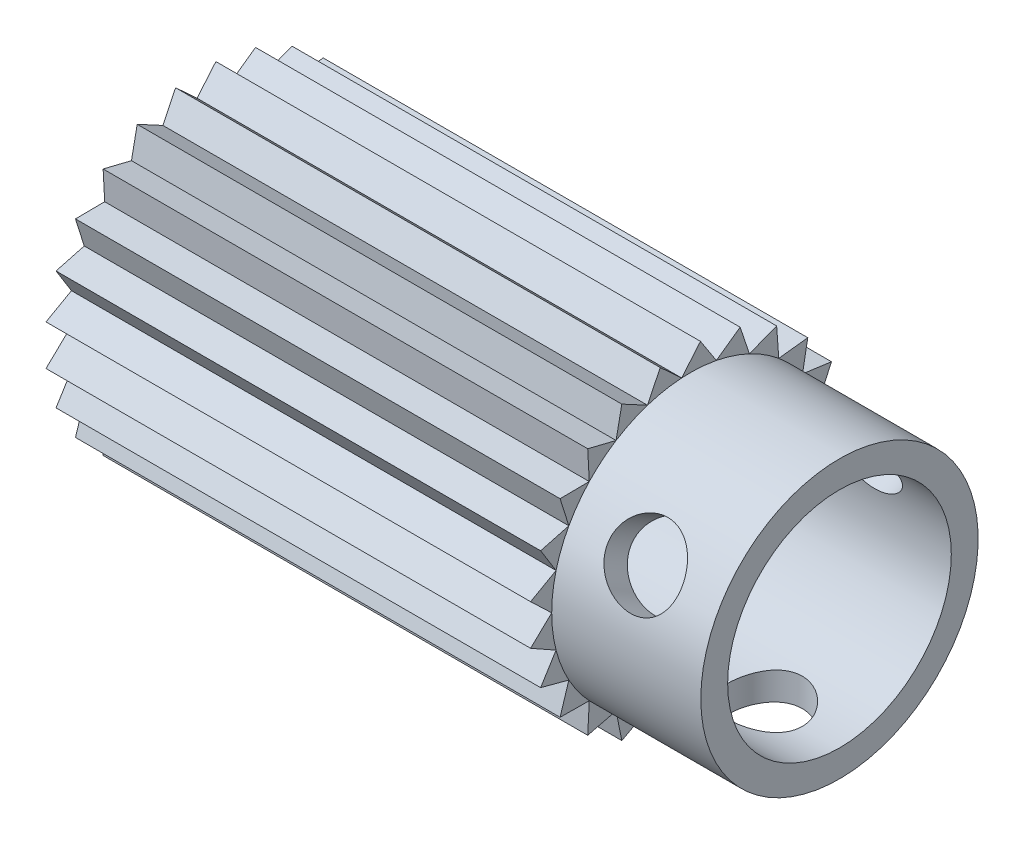
SolidWorks part; units mm, degrees
material "AISI 1020"
ref_plane "X-Y Datum" through (0, 0, 0) normal (0, 0, 1) x (1, 0, 0)
ref_plane "X-Z Datum" through (0, 0, 0) normal (0, 1, 0) x (1, 0, 0)
ref_plane "Y-Z Datum" through (0, 0, 0) normal (1, 0, 0) x (0, 0, -1)
sketch "Sketch1" plane through (0, 0, 0) normal (0, 1, 0) x (1, 0, 0)
  line L0 (-42.0666, 0) -> (42.0666, 0) construction
  line L1 (-30.1625, -15.875) -> (-30.1625, -6.35)
  line L3 (23.8125, -9.525) -> (23.8125, -11.811)
  line L4 (23.8125, -11.811) -> (11.1125, -11.811)
  line L5 (11.1125, -11.811) -> (11.1125, -15.875)
  line L6 (11.1125, -15.875) -> (-30.1625, -15.875)
  line L7 (-30.1625, -6.35) -> (-23.8125, -6.35)
  line L8 (-23.8125, -6.35) -> (-23.8125, -9.525)
  line L9 (-23.8125, -9.525) -> (23.8125, -9.525)
  point P4 (0, -9.525)
  dimension "D1" = 41.275
  dimension "D2" = 6.35
  dimension "D3" = 6.35
  dimension "D4" = 9.525
  dimension "D5" = 11.811
  dimension "D6" = 15.875
  dimension "D7" = 53.975
revolve "Revolve1" add sketch "Sketch1" angle 360 about L0
sketch "Sketch2" plane through (0, 0, 0) normal (0, 1, 0) x (1, 0, 0)
  line L0 (23.8125, -11.811) -> (11.1125, -11.811) construction
  circle A0 centre (17.4625, 0) radius 3.175
  point P7 (17.4625, -11.811)
  dimension "D1" = 6.35
extrude "Cut-Extrude1" cut sketch "Sketch2" against normal through all
pattern_circular "CirPattern1" count 3 over 360 about axis through (-42.0666, 0, 0) along (1, 0, 0) of "Cut-Extrude1"
sketch "Sketch3" plane through (-30.1625, 0, 0) normal (-1, 0, 0) x (0, 0, 1)
  line L0 (0, 0) -> (15.875, 0) construction
  line L2 (15.7498, 1.9897) -> (0, 0) construction
  line L3 (0, 0) -> (15.3763, 3.948) construction
  line L4 (11.811, 0) -> (13.6078, 1.7191)
  line L5 (13.6078, 1.7191) -> (11.4399, 2.9373)
  line L6 (13.6078, -1.7191) -> (11.811, 0)
  line L7 (11.4399, -2.9373) -> (13.6078, -1.7191)
  line L8 (12.7528, -5.0492) -> (11.4399, -2.9373)
  line L9 (10.3501, -5.69) -> (12.7528, -5.0492)
  line L10 (11.0965, -8.0621) -> (10.3501, -5.69)
  line L11 (8.6098, -8.0852) -> (11.0965, -8.0621)
  line L12 (8.7429, -10.5684) -> (8.6098, -8.0852)
  line L13 (6.3287, -9.9724) -> (8.7429, -10.5684)
  line L14 (5.84, -12.4106) -> (6.3287, -9.9724)
  line L15 (3.6498, -11.2329) -> (5.84, -12.4106)
  line L16 (2.5701, -13.4731) -> (3.6498, -11.2329)
  line L17 (0.7416, -11.7877) -> (2.5701, -13.4731)
  line L18 (-0.8612, -13.6889) -> (0.7416, -11.7877)
  line L19 (-2.2132, -11.6018) -> (-0.8612, -13.6889)
  line L20 (-4.2385, -13.0447) -> (-2.2132, -11.6018)
  line L21 (-5.0289, -10.6869) -> (-4.2385, -13.0447)
  line L22 (-7.3494, -11.5808) -> (-5.0289, -10.6869)
  line L23 (-7.5286, -9.1005) -> (-7.3494, -11.5808)
  line L24 (-9.9985, -9.3892) -> (-7.5286, -9.1005)
  line L25 (-9.5553, -6.9423) -> (-9.9985, -9.3892)
  line L26 (-12.0194, -6.6077) -> (-9.5553, -6.9423)
  line L27 (-10.9816, -4.3479) -> (-12.0194, -6.6077)
  line L28 (-13.2851, -3.411) -> (-10.9816, -4.3479)
  line L29 (-11.7179, -1.4803) -> (-13.2851, -3.411)
  line L30 (-13.716, 0) -> (-11.7179, -1.4803)
  line L31 (-11.7179, 1.4803) -> (-13.716, 0)
  line L32 (-13.2851, 3.411) -> (-11.7179, 1.4803)
  line L33 (-10.9816, 4.3479) -> (-13.2851, 3.411)
  line L34 (-12.0194, 6.6077) -> (-10.9816, 4.3479)
  line L35 (-9.5553, 6.9423) -> (-12.0194, 6.6077)
  line L36 (-9.9985, 9.3892) -> (-9.5553, 6.9423)
  line L37 (-7.5286, 9.1005) -> (-9.9985, 9.3892)
  line L38 (-7.3494, 11.5808) -> (-7.5286, 9.1005)
  line L39 (-5.0289, 10.6869) -> (-7.3494, 11.5808)
  line L40 (-4.2385, 13.0447) -> (-5.0289, 10.6869)
  line L41 (-2.2132, 11.6018) -> (-4.2385, 13.0447)
  line L42 (-0.8612, 13.6889) -> (-2.2132, 11.6018)
  line L43 (0.7416, 11.7877) -> (-0.8612, 13.6889)
  line L44 (2.5701, 13.4731) -> (0.7416, 11.7877)
  line L45 (3.6498, 11.2329) -> (2.5701, 13.4731)
  line L46 (5.84, 12.4106) -> (3.6498, 11.2329)
  line L47 (6.3287, 9.9724) -> (5.84, 12.4106)
  line L48 (8.7429, 10.5684) -> (6.3287, 9.9724)
  line L49 (8.6098, 8.0852) -> (8.7429, 10.5684)
  line L50 (11.0965, 8.0621) -> (8.6098, 8.0852)
  line L51 (10.3501, 5.69) -> (11.0965, 8.0621)
  line L52 (12.7528, 5.0492) -> (10.3501, 5.69)
  line L53 (11.4399, 2.9373) -> (12.7528, 5.0492)
  circle A0 centre (0, 0) radius 15.875 construction
  circle A1 centre (0, 0) radius 11.811 construction
  circle A2 centre (0, 0) radius 13.716 construction
  circle A3 centre (0, 0) radius 11.811 construction
  arc A4 (11.811, 0) -> (11.4399, 2.9373) centre (0, 0) ccw
  arc A5 (11.4399, -2.9373) -> (11.811, 0) centre (0, 0) ccw
  arc A6 (10.3501, -5.69) -> (11.4399, -2.9373) centre (0, 0) ccw
  arc A7 (8.6098, -8.0852) -> (10.3501, -5.69) centre (0, 0) ccw
  arc A8 (6.3287, -9.9724) -> (8.6098, -8.0852) centre (0, 0) ccw
  arc A9 (3.6498, -11.2329) -> (6.3287, -9.9724) centre (0, 0) ccw
  arc A10 (0.7416, -11.7877) -> (3.6498, -11.2329) centre (0, 0) ccw
  arc A11 (-2.2132, -11.6018) -> (0.7416, -11.7877) centre (0, 0) ccw
  arc A12 (-5.0289, -10.6869) -> (-2.2132, -11.6018) centre (0, 0) ccw
  arc A13 (-7.5286, -9.1005) -> (-5.0289, -10.6869) centre (0, 0) ccw
  arc A14 (-9.5553, -6.9423) -> (-7.5286, -9.1005) centre (0, 0) ccw
  arc A15 (-10.9816, -4.3479) -> (-9.5553, -6.9423) centre (0, 0) ccw
  arc A16 (-11.7179, -1.4803) -> (-10.9816, -4.3479) centre (0, 0) ccw
  arc A17 (-11.7179, 1.4803) -> (-11.7179, -1.4803) centre (0, 0) ccw
  arc A18 (-10.9816, 4.3479) -> (-11.7179, 1.4803) centre (0, 0) ccw
  arc A19 (-9.5553, 6.9423) -> (-10.9816, 4.3479) centre (0, 0) ccw
  arc A20 (-7.5286, 9.1005) -> (-9.5553, 6.9423) centre (0, 0) ccw
  arc A21 (-5.0289, 10.6869) -> (-7.5286, 9.1005) centre (0, 0) ccw
  arc A22 (-2.2132, 11.6018) -> (-5.0289, 10.6869) centre (0, 0) ccw
  arc A23 (0.7416, 11.7877) -> (-2.2132, 11.6018) centre (0, 0) ccw
  arc A24 (3.6498, 11.2329) -> (0.7416, 11.7877) centre (0, 0) ccw
  arc A25 (6.3287, 9.9724) -> (3.6498, 11.2329) centre (0, 0) ccw
  arc A26 (8.6098, 8.0852) -> (6.3287, 9.9724) centre (0, 0) ccw
  arc A27 (10.3501, 5.69) -> (8.6098, 8.0852) centre (0, 0) ccw
  arc A28 (11.4399, 2.9373) -> (10.3501, 5.69) centre (0, 0) ccw
  circle A29 centre (0, 0) radius 15.875
  circle M6 centre (0, 0) radius 15.875
  dimension "D3" = 1.905
  dimension "D4" = 25
  dimension "D1" = 7.2
  dimension "D2" = 14.4
extrude "Cut-Extrude2" cut sketch "Sketch3" against normal through all contours L53 L5 L4 L6 L7 L8 L9 L10 L11 L12 L13 L14 L15 L16 L17 L18 L19 L20 L21 L22 L23 L24 L25 L26 L27 L28 L29 L30 L31 L32 L33 L34 L35 L36 L37 L38 L39 L40 L41 L42 L43 L44 L45 L46 L47 L48 L49 L50 L51 M6
